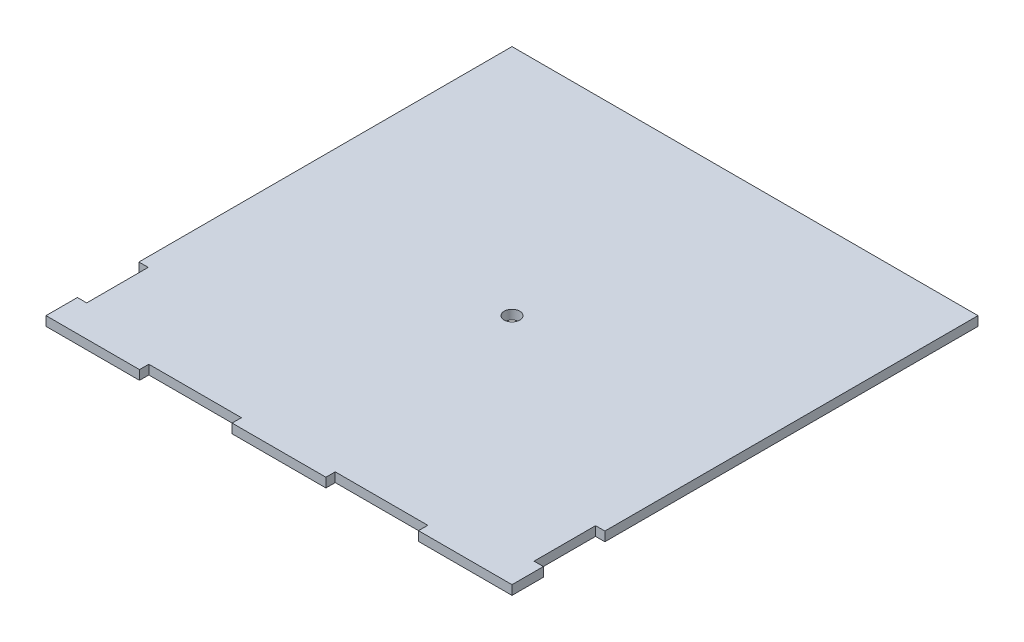
SolidWorks part; units mm, degrees
ref_plane "Front Plane" through (0, 0, 0) normal (0, 0, 1) x (1, 0, 0)
ref_plane "Top Plane" through (0, 0, 0) normal (0, 1, 0) x (1, 0, 0)
ref_plane "Right Plane" through (0, 0, 0) normal (1, 0, 0) x (0, 0, -1)
sketch "Sketch1" plane through (0, 0, 0) normal (0, 1, 0) x (1, 0, 0)
  line L0 (90.1, 0) -> (90.1, 3)
  line L1 (0, 0) -> (150, 0)
  line L2 (0, 0) -> (0, 150)
  line L3 (0, 150) -> (150, 150)
  line L4 (150, 0) -> (150, 150)
  line L5 (30.1, 0) -> (59.9, 0)
  line L6 (30.1, 0) -> (30.1, 3)
  line L7 (30.1, 3) -> (59.9, 3)
  line L8 (59.9, 0) -> (59.9, 3)
  line L9 (90.1, 0) -> (119.9, 0)
  line L10 (119.9, 0) -> (119.9, 3)
  line L11 (90.1, 3) -> (119.9, 3)
  line L12 (-850, 75) -> (49150, 75) construction
  line L13 (75, -850) -> (75, 49150) construction
  line L14 (0, 10.1) -> (3, 10.1)
  line L15 (150, 29.9) -> (147, 29.9)
  line L16 (150, 29.9) -> (150, 10.1)
  line L17 (150, 10.1) -> (147, 10.1)
  line L18 (147, 29.9) -> (147, 10.1)
  line L19 (3, 29.9) -> (3, 10.1)
  line L20 (0, 29.9) -> (3, 29.9)
  line L21 (0, 29.9) -> (0, 10.1)
  circle A0 centre (75, 75) radius 2.5
  point P16 (150, 75)
  point P19 (75, 150)
  dimension "D8" = 5
  dimension "D1" = 150
  dimension "D2" = 150
  dimension "D3" = 29.8
  dimension "D4" = 30.1
  dimension "D5" = 3
  dimension "D7" = 30.2
  dimension "D9" = 19.8
  dimension "D10" = 10.1
  dimension "D11" = 3
  dimension "D6" = 2
extrude "Boss-Extrude1" add sketch "Sketch1" along normal blind 3 contours L2 L20 L19 L14 L1 L6 L7 L8 L0 L11 L10 L4 L17 L18 L15 L3 A0
